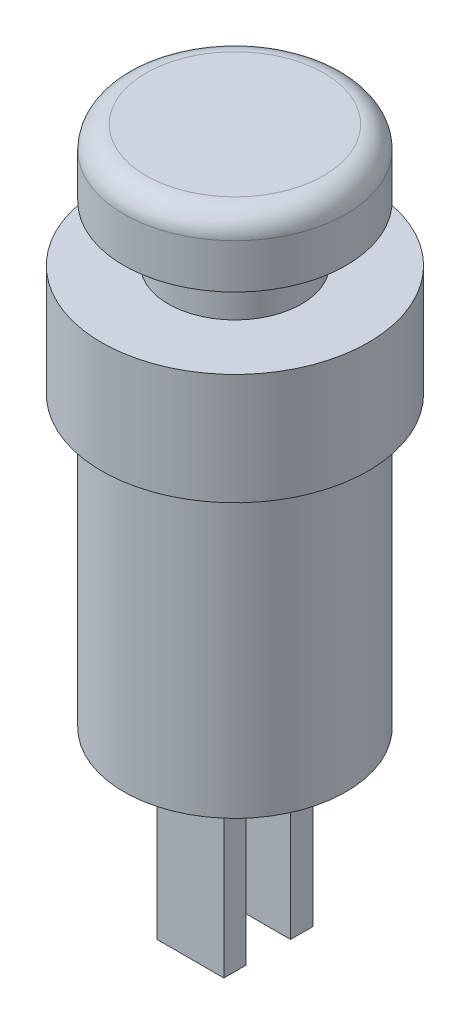
SolidWorks part; units mm, degrees
ref_plane "Plan de face" through (0, 0, 0) normal (0, 0, 1) x (1, 0, 0)
ref_plane "Plan de dessus" through (0, 0, 0) normal (0, 1, 0) x (1, 0, 0)
ref_plane "Plan de droite" through (0, 0, 0) normal (1, 0, 0) x (0, 0, -1)
sketch "Esquisse1" plane through (0, 0, 0) normal (0, 0, 1) x (1, 0, 0)
  line L0 (0, 0) -> (0, 42.0186) construction
  line L1 (0, 0) -> (-5, 0)
  line L2 (-5, 0) -> (-5, 13)
  line L3 (-5, 13) -> (-6, 13)
  line L4 (-6, 13) -> (-6, 18)
  line L5 (-6, 18) -> (-3, 18)
  line L6 (0, 20.5) -> (0, 0)
  line L7 (-3, 18) -> (-3, 20.5)
  line L8 (-3, 20.5) -> (0, 20.5)
  dimension "D1" = 5
  dimension "D2" = 6
  dimension "D3" = 18
  dimension "D4" = 5
  dimension "D5" = 3
  dimension "D6" = 2.5
revolve "Révolution1" add sketch "Esquisse1" angle 360 about L0
sketch "Esquisse2" plane through (0, 0, 0) normal (0, 0, 1) x (1, 0, 0)
  line L0 (0, 20.5) -> (0, 26.1439) construction
  line L1 (3, 20.5) -> (-3, 20.5) construction
  line L2 (0, 20.5) -> (-5, 20.5)
  line L3 (-5, 20.5) -> (-5, 22.5)
  line L4 (-4, 23.5) -> (0, 23.5)
  line L5 (0, 23.5) -> (0, 20.5)
  arc A0 (-4, 23.5) -> (-5, 22.5) centre (-4, 22.5) ccw
  dimension "D1" = 1
  dimension "D2" = 3
  dimension "D3" = 5
revolve "Révolution2" add sketch "Esquisse2" angle 360 about L0
sketch "Esquisse3" plane through (0, 0, 0) normal (0, -1, 0) x (1, 0, 0)
  line L1 (-1.5, -2) -> (1.5, -2)
  line L2 (-1.5, -2) -> (-1.5, -1)
  line L3 (-1.5, -1) -> (1.5, -1)
  line L4 (1.5, -2) -> (1.5, -1)
  line L5 (-1.5, 1) -> (1.5, 1)
  line L6 (-1.5, 1) -> (-1.5, 2)
  line L7 (-1.5, 2) -> (1.5, 2)
  line L8 (1.5, 1) -> (1.5, 2)
  dimension "D1" = 1
  dimension "D2" = 1
  dimension "D3" = 1
  dimension "D4" = 3
  dimension "D5" = 1.5
extrude "Boss.-Extru.1" add sketch "Esquisse3" along normal blind 8
